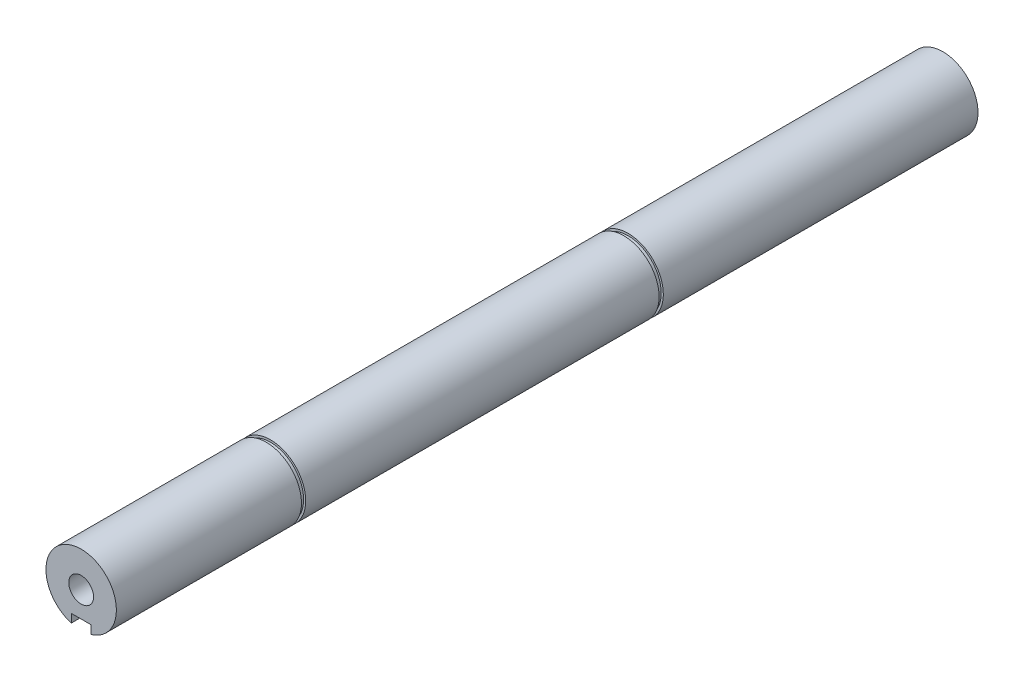
SolidWorks part; units mm, degrees
material "AISI 1020"
ref_plane "Спереди" through (0, 0, 0) normal (0, 0, 1) x (1, 0, 0)
ref_plane "Сверху" through (0, 0, 0) normal (0, 1, 0) x (1, 0, 0)
ref_plane "Справа" through (0, 0, 0) normal (1, 0, 0) x (0, 0, -1)
sketch "Эскиз1" plane through (0, 0, 0) normal (0, 0, 1) x (1, 0, 0)
  circle A0 centre (0, 0) radius 12.5
  dimension "D1" = 25
extrude "Бобышка-Вытянуть1" add sketch "Эскиз1" against normal up to surface (305.8363 mm away)
sketch "Эскиз2" plane through (0, 0, 0) normal (0, 0, 1) x (1, 0, 0)
  line L0 (3.5, -16) -> (3.5, -9) construction
  line L1 (-3.5, -16) -> (3.5, -16) construction
  line L2 (-3.5, -9) -> (-3.5, -16) construction
  line L3 (3.5, -9) -> (-3.5, -9) construction
  line L4 (3.5, -16) -> (3.5, -9)
  line L5 (-3.5, -16) -> (3.5, -16)
  line L6 (-3.5, -9) -> (-3.5, -16)
  line L7 (3.5, -9) -> (-3.5, -9)
extrude "Вырез-Вытянуть1" cut sketch "Эскиз2" against normal up to surface (31.8 mm away)
sketch "Эскиз3" plane through (0, 0, -305.8363) normal (0, 0, -1) x (-1, 0, 0)
  line L0 (-3.5, -16) -> (3.5, -16) construction
  line L1 (3.5, -16) -> (3.5, -9) construction
  line L2 (3.5, -9) -> (-3.5, -9) construction
  line L3 (-3.5, -9) -> (-3.5, -16) construction
  line L4 (-3.5, -16) -> (3.5, -16)
  line L5 (3.5, -16) -> (3.5, -9)
  line L6 (3.5, -9) -> (-3.5, -9)
  line L7 (-3.5, -9) -> (-3.5, -16)
extrude "Вырез-Вытянуть2" cut sketch "Эскиз3" against normal up to surface (112 mm away)
hole_wizard "Отверстие обработанное метчиком M10x1.251" positions "Эскиз4" profile "Эскиз5" tap size "M10x1.25" standard "ISO"
sketch "Эскиз4" plane through (0, 0, 0) normal (0, 0, 1) x (1, 0, 0)
  point P0 (0, 0)
sketch "Эскиз5" plane through (0, 0, 0) normal (1, 0, 0) x (0, -1, 0)
  line L0 (0, 0) -> (0, 28.8938)
  line L1 (0, 28.8938) -> (4.4, 26.25)
  line L2 (4.4, 26.25) -> (4.4, 0)
  line L5 (4.4, 0) -> (0, 0)
  line L10 (0, 28.8938) -> (-4.4, 26.25) construction
  line L11 (0, -6.35) -> (0, 107.95) construction
  dimension "Диаметр сверла" = 8.8
  dimension "Глубина сверла" = 26.25
  dimension "Угол заточки сверла" = 118
cosmetic thread "Отверстие резьбы1" parameters "D1"=20, "D2"=10
hole_wizard "Отверстие обработанное метчиком M10x1.252" positions "Эскиз6" profile "Эскиз7" tap size "M10x1.25" standard "ISO"
sketch "Эскиз6" plane through (0, 0, -305.8363) normal (0, 0, -1) x (-1, 0, 0)
  point P0 (0, 0)
sketch "Эскиз7" plane through (0, 0, -305.8363) normal (1, 0, 0) x (0, 1, 0)
  line L0 (0, 0) -> (0, 28.8938)
  line L1 (0, 28.8938) -> (4.4, 26.25)
  line L2 (4.4, 26.25) -> (4.4, 0)
  line L5 (4.4, 0) -> (0, 0)
  line L10 (0, 28.8938) -> (-4.4, 26.25) construction
  line L11 (0, -6.35) -> (0, 107.95) construction
  dimension "Диаметр сверла" = 8.8
  dimension "Глубина сверла" = 26.25
  dimension "Угол заточки сверла" = 118
cosmetic thread "Отверстие резьбы2" parameters "D1"=20, "D2"=10
sketch "Эскиз8" plane through (0, 0, 0) normal (1, 0, 0) x (0, 0, -1)
  line L0 (-1000, 0) -> (49000, 0) construction
  line L1 (67.2, 11.75) -> (65.7, 11.75)
  line L2 (65.7, 11.75) -> (65.7, 12.5)
  line L3 (65.5, 12.5) -> (32.3, 12.5) construction
  line L4 (65.7, 12.5) -> (67.2, 12.5)
  line L5 (67.2, 17.4) -> (67.2, -17.4) construction
  line L6 (305.8363, 12.5) -> (0, 12.5) construction
  line L7 (192.6363, 11.75) -> (194.1363, 11.75)
  line L8 (194.1363, 11.75) -> (194.1363, 12.5)
  line L9 (305.8363, 12.5) -> (193.8363, 12.5) construction
  line L10 (194.1363, 12.5) -> (192.6363, 12.5)
  line L11 (192.6363, 14.7161) -> (192.6363, -9.7325) construction
  line L12 (192.6363, 12.5) -> (192.6363, 11.75)
  line L13 (67.2, 12.5) -> (67.2, 11.75)
  dimension "D1" = 1.5
revolve "Вырез-Повернуть1" cut sketch "Эскиз8" angle 360 about L0
